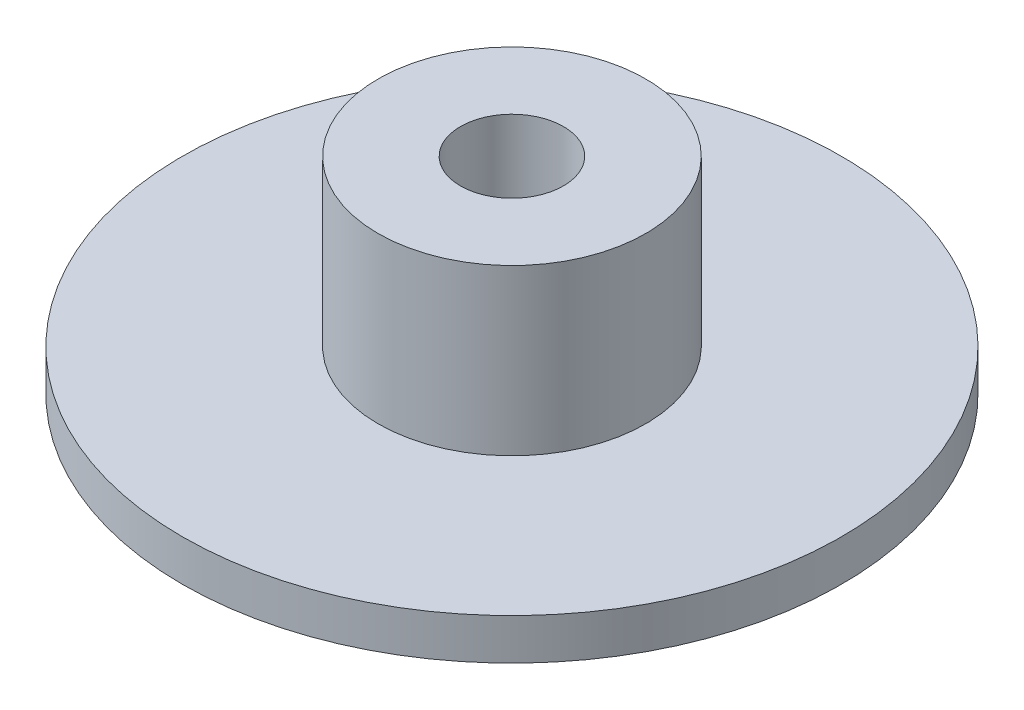
SolidWorks part; units mm, degrees
ref_plane "Спереди" through (0, 0, 0) normal (0, 0, 1) x (1, 0, 0)
ref_plane "Сверху" through (0, 0, 0) normal (0, 1, 0) x (1, 0, 0)
ref_plane "Справа" through (0, 0, 0) normal (1, 0, 0) x (0, 0, -1)
sketch "Эскиз2" plane through (0, 0, 0) normal (0, 1, 0) x (1, 0, 0)
  circle A0 centre (0, 0) radius 16
  circle A1 centre (0, 0) radius 2.5
  dimension "D1" = 32
  dimension "D2" = 5
extrude "Бобышка-Вытянуть1" add sketch "Эскиз2" along normal blind 2
sketch "Эскиз3" plane through (0, 2, 0) normal (0, 1, 0) x (1, 0, 0)
  circle A0 centre (0, 0) radius 6.5
  circle A1 centre (0, 0) radius 2.5
  dimension "D1" = 5
  dimension "D2" = 13
extrude "Бобышка-Вытянуть2" add sketch "Эскиз3" along normal blind 8
